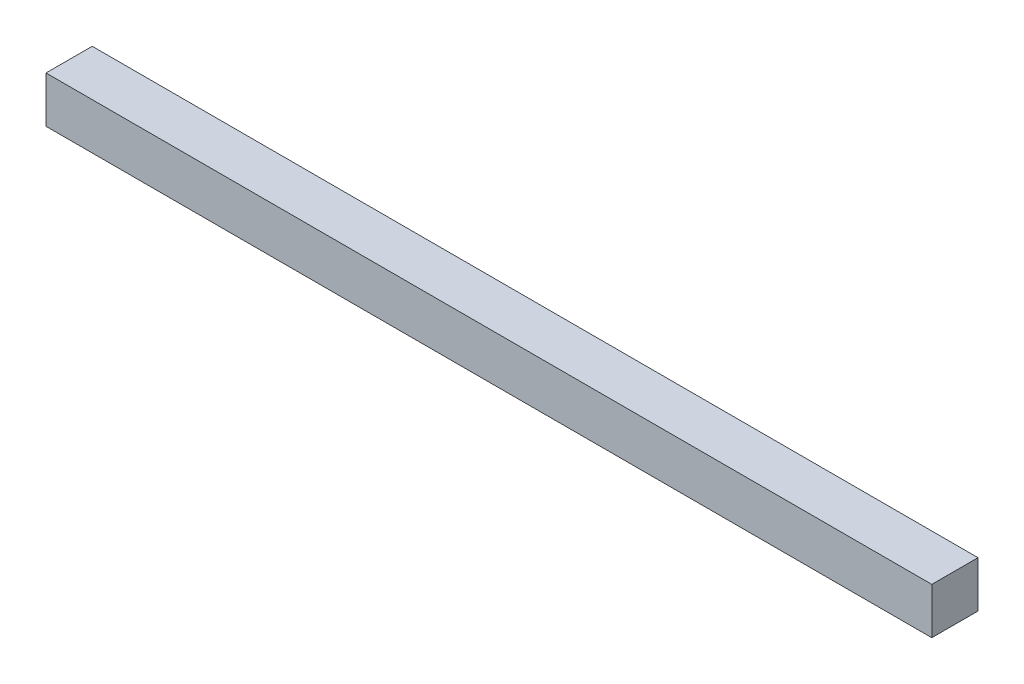
SolidWorks part; units mm, degrees
ref_plane "Front Plane" through (0, 0, 0) normal (0, 0, 1) x (1, 0, 0)
ref_plane "Top Plane" through (0, 0, 0) normal (0, 1, 0) x (1, 0, 0)
ref_plane "Right Plane" through (0, 0, 0) normal (1, 0, 0) x (0, 0, -1)
sketch "Sketch1" plane through (0, 0, 0) normal (0, 1, 0) x (1, 0, 0)
  line L1 (-5.75, -0.3) -> (5.75, -0.3)
  line L2 (-5.75, -0.3) -> (-5.75, 0.3)
  line L3 (-5.75, 0.3) -> (5.75, 0.3)
  line L4 (5.75, -0.3) -> (5.75, 0.3)
  line L5 (-5.75, -0.3) -> (5.75, 0.3) construction
  line L6 (-5.75, 0.3) -> (5.75, -0.3) construction
  point P0 (0, 0)
  dimension "D1" = 0.6
  dimension "D2" = 11.5
extrude "Boss-Extrude2" add sketch "Sketch1" along normal mid plane 0.6
